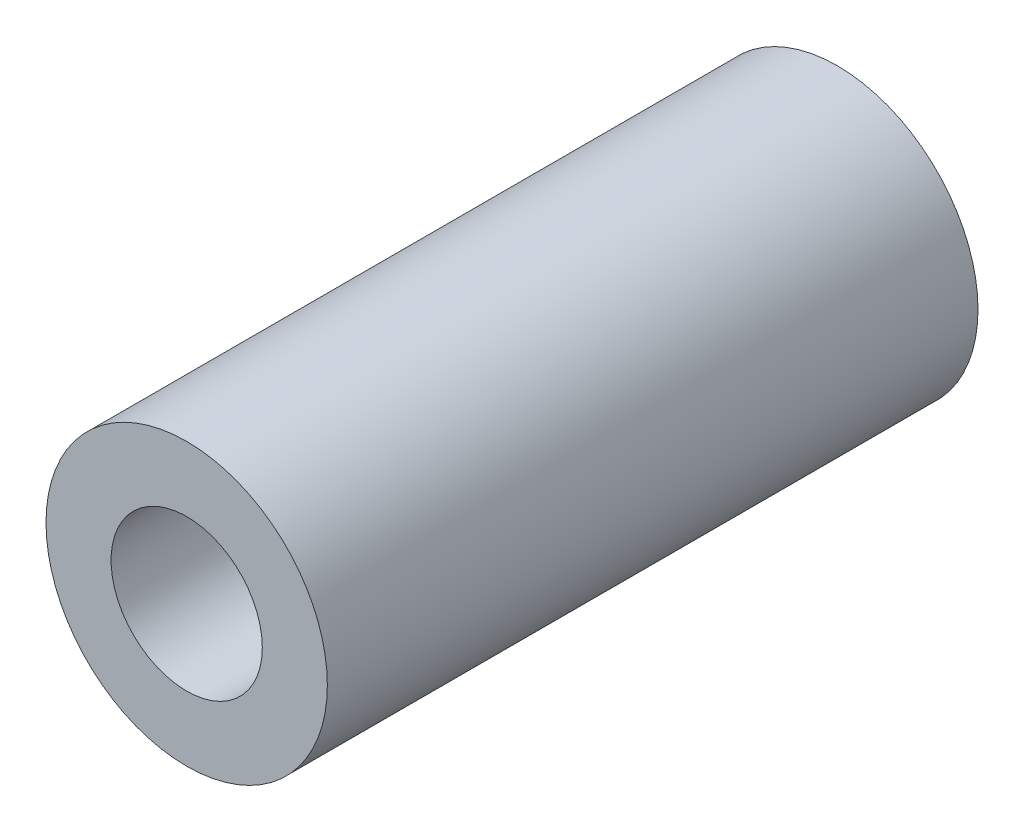
SolidWorks part; units mm, degrees
ref_plane "Front Plane" through (0, 0, 0) normal (0, 0, 1) x (1, 0, 0)
ref_plane "Top Plane" through (0, 0, 0) normal (0, 1, 0) x (1, 0, 0)
ref_plane "Right Plane" through (0, 0, 0) normal (1, 0, 0) x (0, 0, -1)
sketch "Sketch1" plane through (0, 0, 0) normal (0, 0, 1) x (1, 0, 0)
  circle A0 centre (0, 0) radius 2.15
  circle A1 centre (0, 0) radius 4
  dimension "D1" = 4.3
  dimension "D2" = 8
extrude "Boss-Extrude1" add sketch "Sketch1" along normal blind 18.5
